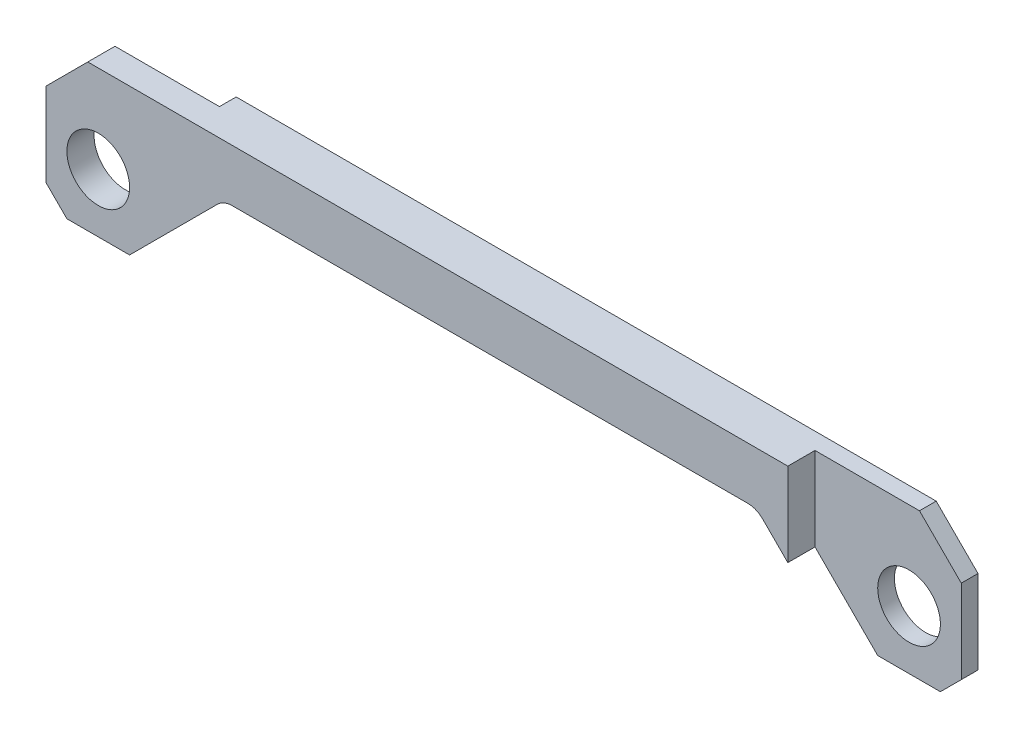
SolidWorks part; units mm, degrees
material "1060 Alloy"
ref_plane "Front Plane" through (0, 0, 0) normal (0, 0, 1) x (1, 0, 0)
ref_plane "Top Plane" through (0, 0, 0) normal (0, 1, 0) x (1, 0, 0)
ref_plane "Right Plane" through (0, 0, 0) normal (1, 0, 0) x (0, 0, -1)
sketch "Sketch4" plane through (0, 0, 0) normal (0, 0, 1) x (1, 0, 0)
  line L0 (38.1, -71.12) -> (-38.1, -71.12)
  line L1 (-63.5, -45.72) -> (-63.5, 55.88)
  line L2 (-12.7, 106.68) -> (965.2, 106.68)
  line L3 (1016, 55.88) -> (1016, -45.72)
  line L4 (990.6, -71.12) -> (914.4, -71.12)
  line L5 (914.4, -71.12) -> (800.1, 43.18)
  line L6 (800.1, 43.18) -> (152.4, 43.18)
  line L7 (152.4, 43.18) -> (38.1, -71.12)
  line L8 (965.2, 106.68) -> (1016, 55.88)
  line L9 (-63.5, 55.88) -> (-12.7, 106.68)
  line L10 (1016, -45.72) -> (990.6, -71.12)
  line L11 (-38.1, -71.12) -> (-63.5, -45.72)
  circle A0 centre (0, 0) radius 38.1
  circle A1 centre (952.5, 0) radius 38.1
  point P6 (-63.5, -71.12)
  point P8 (-63.5, 106.68)
  point P9 (1016, 106.68)
  point P10 (1016, -71.12)
  dimension "D3" = 76.2
  dimension "D1" = 1079.5
  dimension "D2" = 952.5
  dimension "D4" = 71.12
  dimension "D5" = 177.8
  dimension "D6" = 114.3
  dimension "D7" = 63.5
  dimension "D8" = 101.6
  dimension "D9" = 45
  dimension "D10" = 50.8
  dimension "D11" = 45
  dimension "D12" = 50.8
  dimension "D13" = 45
  dimension "D14" = 25.4
  dimension "D15" = 45
  dimension "D16" = 25.4
  dimension "D17" = 45
extrude "Base" add sketch "Sketch4" along normal blind 53.34
sketch "Sketch5" plane through (0, 106.68, 0) normal (0, 1, 0) x (1, 0, 0)
  line L0 (-63.5, -53.34) -> (-63.5, 0) construction
  line L1 (-63.5, 0) -> (114.3, 0)
  line L2 (-63.5, 0) -> (-63.5, -20.32)
  line L3 (-63.5, -20.32) -> (114.3, -20.32)
  line L4 (114.3, 0) -> (114.3, -20.32)
  line L5 (1016, -53.34) -> (838.2, -53.34)
  line L6 (1016, -53.34) -> (1016, -20.32)
  line L7 (1016, -20.32) -> (838.2, -20.32)
  line L8 (838.2, -53.34) -> (838.2, -20.32)
  line L9 (965.2, -53.34) -> (-12.7, -53.34) construction
  line L10 (965.2, 0) -> (-12.7, 0) construction
  point P12 (838.2, -36.83)
  dimension "D1" = 177.8
  dimension "D2" = 901.7
  dimension "D3" = 33.02
  dimension "D4" = 20.32
extrude "side cuts" cut sketch "Sketch5" against normal through all
fillet "bottom fillet" radius 25.4 2 edges at (152.4, 43.18, 26.67) (800.1, 43.18, 26.67)
